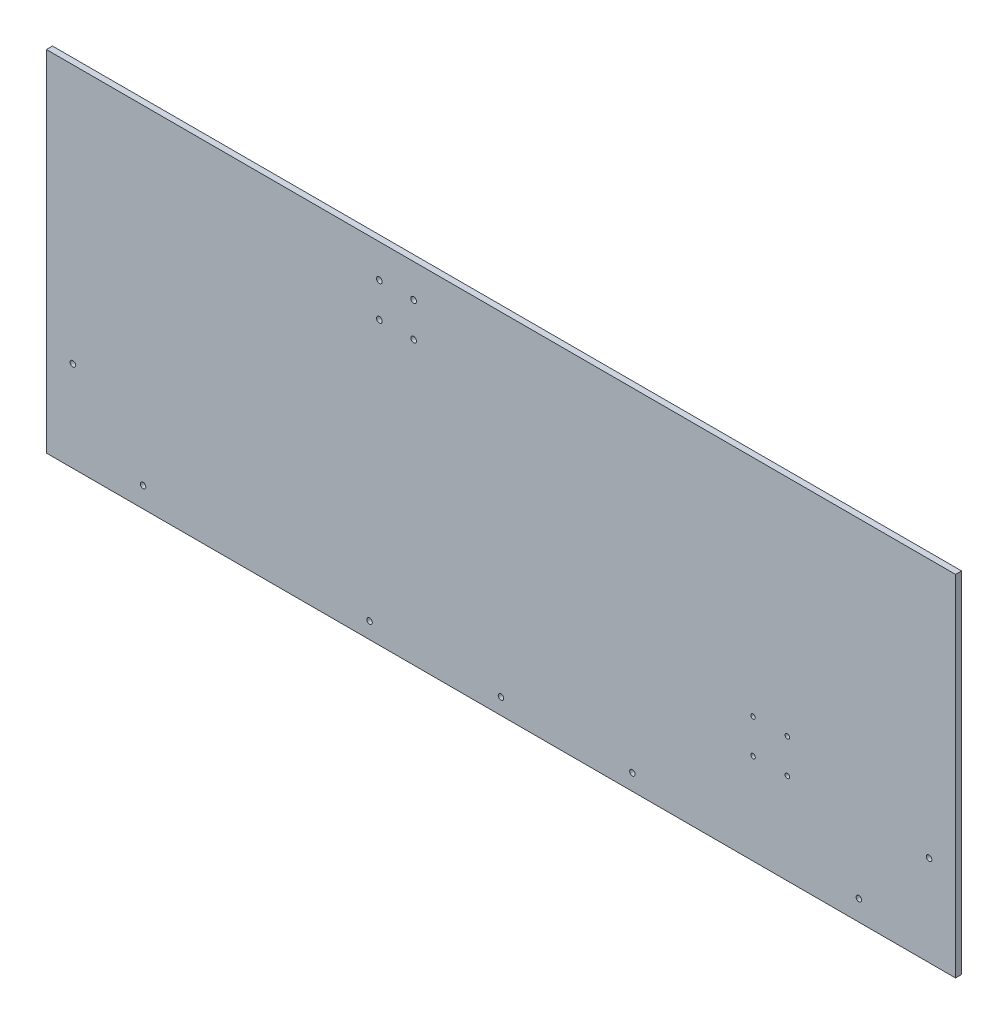
SolidWorks part; units mm, degrees
ref_plane "Front Plane" through (0, 0, 0) normal (0, 0, 1) x (1, 0, 0)
ref_plane "Top Plane" through (0, 0, 0) normal (0, 1, 0) x (1, 0, 0)
ref_plane "Right Plane" through (0, 0, 0) normal (1, 0, 0) x (0, 0, -1)
sketch "Sketch1" plane through (0, 0, 0) normal (0, 0, 1) x (1, 0, 0)
  line L1 (-357.1875, -137.3187) -> (357.1875, -137.3187)
  line L2 (-357.1875, -137.3187) -> (-357.1875, 137.3188)
  line L3 (-357.1875, 137.3188) -> (357.1875, 137.3188)
  line L4 (357.1875, -137.3187) -> (357.1875, 137.3188)
  line L5 (-357.1875, -137.3187) -> (357.1875, 137.3188) construction
  line L6 (-357.1875, 137.3188) -> (357.1875, -137.3187) construction
  point P0 (0, 0)
  dimension "D1" = 714.375
  dimension "D2" = 274.6375
extrude "Boss-Extrude1" add sketch "Sketch1" along normal blind 4.7625
sketch "Sketch2" plane through (0, 0, 4.7625) normal (0, 0, 1) x (1, 0, 0)
  line L0 (-357.1875, -137.3187) -> (-357.1875, -73.8187) construction
  line L1 (-357.1875, 137.3188) -> (-357.1875, -137.3187) construction
  line L2 (-357.1875, -105.5687) -> (357.1875, -105.5687) construction
  line L3 (12.286, -89.5705) -> (10.3514, -91.5051)
  line L4 (0, -105.5687) -> (0, -137.3187) construction
  line L5 (-357.1875, -137.3187) -> (357.1875, -137.3187) construction
  line L6 (357.1875, -137.3187) -> (357.1875, 137.3188) construction
  line L7 (0, -105.5687) -> (14.1421, -91.4266) construction
  line L8 (14.1421, -91.4266) -> (12.286, -89.5705) construction
  line L9 (12.286, -89.5705) -> (15.9983, -93.2828) construction
  line L10 (15.9983, -93.2828) -> (14.0637, -95.2174)
  line L11 (15.9983, -117.8547) -> (14.0637, -115.9201)
  line L12 (12.286, -121.567) -> (10.3514, -119.6324)
  line L13 (0, -105.5687) -> (14.1421, -119.7109) construction
  line L14 (14.1421, -119.7109) -> (15.9983, -117.8547) construction
  line L15 (15.9983, -117.8547) -> (12.286, -121.567) construction
  line L16 (-12.286, -121.567) -> (-10.3514, -119.6324)
  line L17 (-15.9983, -117.8547) -> (-14.0637, -115.9201)
  line L18 (0, -105.5687) -> (-14.1421, -119.7109) construction
  line L19 (-14.1421, -119.7109) -> (-12.286, -121.567) construction
  line L20 (-12.286, -121.567) -> (-15.9983, -117.8547) construction
  line L21 (-15.9983, -93.2828) -> (-14.0637, -95.2174)
  line L22 (-12.286, -89.5705) -> (-10.3514, -91.5051)
  line L23 (0, -105.5687) -> (-14.1421, -91.4266) construction
  line L24 (-14.1421, -91.4266) -> (-15.9983, -93.2828) construction
  line L25 (-15.9983, -93.2828) -> (-12.286, -89.5705) construction
  line L26 (0, -105.5687) -> (-317.5, -105.5687) construction
  line L27 (0, -105.5687) -> (317.5, -105.5687) construction
  line L28 (-317.5, -105.5687) -> (0, -105.5687) construction
  line L29 (-158.75, -105.5687) -> (-158.75, 137.3188) construction
  line L30 (357.1875, 137.3188) -> (-357.1875, 137.3188) construction
  line L31 (317.5, -105.5687) -> (0, -105.5687) construction
  line L32 (158.75, -105.5687) -> (158.75, 137.3188) construction
  line L33 (-301.5017, -93.2828) -> (-305.214, -89.5705) construction
  line L34 (-303.3579, -91.4266) -> (-301.5017, -93.2828) construction
  line L35 (-317.5, -105.5687) -> (-303.3579, -91.4266) construction
  line L36 (-305.214, -121.567) -> (-301.5017, -117.8547) construction
  line L37 (-303.3579, -119.7109) -> (-305.214, -121.567) construction
  line L38 (-317.5, -105.5687) -> (-303.3579, -119.7109) construction
  line L39 (-333.4983, -117.8547) -> (-329.786, -121.567) construction
  line L40 (-331.6421, -119.7109) -> (-333.4983, -117.8547) construction
  line L41 (-317.5, -105.5687) -> (-331.6421, -119.7109) construction
  line L42 (-329.786, -89.5705) -> (-333.4983, -93.2828) construction
  line L43 (-331.6421, -91.4266) -> (-329.786, -89.5705) construction
  line L44 (-317.5, -105.5687) -> (-331.6421, -91.4266) construction
  line L45 (-317.5, -105.5687) -> (-317.5, -137.3187) construction
  line L46 (-305.214, -89.5705) -> (-307.1486, -91.5051)
  line L47 (-301.5017, -93.2828) -> (-303.4363, -95.2174)
  line L48 (-301.5017, -117.8547) -> (-303.4363, -115.9201)
  line L49 (-305.214, -121.567) -> (-307.1486, -119.6324)
  line L50 (-329.786, -121.567) -> (-327.8514, -119.6324)
  line L51 (-333.4983, -117.8547) -> (-331.5637, -115.9201)
  line L52 (-333.4983, -93.2828) -> (-331.5637, -95.2174)
  line L53 (-329.786, -89.5705) -> (-327.8514, -91.5051)
  line L54 (333.4983, -93.2828) -> (329.786, -89.5705) construction
  line L55 (331.6421, -91.4266) -> (333.4983, -93.2828) construction
  line L56 (317.5, -105.5687) -> (331.6421, -91.4266) construction
  line L57 (329.786, -121.567) -> (333.4983, -117.8547) construction
  line L58 (331.6421, -119.7109) -> (329.786, -121.567) construction
  line L59 (317.5, -105.5687) -> (331.6421, -119.7109) construction
  line L60 (301.5017, -117.8547) -> (305.214, -121.567) construction
  line L61 (303.3579, -119.7109) -> (301.5017, -117.8547) construction
  line L62 (317.5, -105.5687) -> (303.3579, -119.7109) construction
  line L63 (305.214, -89.5705) -> (301.5017, -93.2828) construction
  line L64 (303.3579, -91.4266) -> (305.214, -89.5705) construction
  line L65 (317.5, -105.5687) -> (303.3579, -91.4266) construction
  line L66 (317.5, -105.5687) -> (317.5, -137.3187) construction
  line L67 (329.786, -89.5705) -> (327.8514, -91.5051)
  line L68 (333.4983, -93.2828) -> (331.5637, -95.2174)
  line L69 (333.4983, -117.8547) -> (331.5637, -115.9201)
  line L70 (329.786, -121.567) -> (327.8514, -119.6324)
  line L71 (305.214, -121.567) -> (307.1486, -119.6324)
  line L72 (301.5017, -117.8547) -> (303.4363, -115.9201)
  line L73 (301.5017, -93.2828) -> (303.4363, -95.2174)
  line L74 (305.214, -89.5705) -> (307.1486, -91.5051)
  arc A0 (-14.0637, -95.2174) -> (-14.0637, -115.9201) centre (0, -105.5687) ccw
  arc A1 (15.9983, -93.2828) -> (12.286, -89.5705) centre (14.1421, -91.4266) ccw
  arc A2 (12.286, -121.567) -> (15.9983, -117.8547) centre (14.1421, -119.7109) ccw
  arc A3 (-15.9983, -117.8547) -> (-12.286, -121.567) centre (-14.1421, -119.7109) ccw
  arc A4 (-12.286, -89.5705) -> (-15.9983, -93.2828) centre (-14.1421, -91.4266) ccw
  arc A5 (10.3514, -91.5051) -> (-10.3514, -91.5051) centre (0, -105.5687) ccw
  arc A6 (14.0637, -115.9201) -> (14.0637, -95.2174) centre (0, -105.5687) ccw
  arc A7 (-10.3514, -119.6324) -> (10.3514, -119.6324) centre (0, -105.5687) ccw
  arc A8 (-307.1486, -119.6324) -> (-327.8514, -119.6324) centre (-317.5, -105.5687) cw
  arc A9 (-331.5637, -115.9201) -> (-331.5637, -95.2174) centre (-317.5, -105.5687) cw
  arc A10 (-327.8514, -91.5051) -> (-307.1486, -91.5051) centre (-317.5, -105.5687) cw
  arc A11 (-305.214, -89.5705) -> (-301.5017, -93.2828) centre (-303.3579, -91.4266) cw
  arc A12 (-301.5017, -117.8547) -> (-305.214, -121.567) centre (-303.3579, -119.7109) cw
  arc A13 (-329.786, -121.567) -> (-333.4983, -117.8547) centre (-331.6421, -119.7109) cw
  arc A14 (-333.4983, -93.2828) -> (-329.786, -89.5705) centre (-331.6421, -91.4266) cw
  arc A15 (-303.4363, -95.2174) -> (-303.4363, -115.9201) centre (-317.5, -105.5687) cw
  arc A16 (327.8514, -119.6324) -> (307.1486, -119.6324) centre (317.5, -105.5687) cw
  arc A17 (303.4363, -115.9201) -> (303.4363, -95.2174) centre (317.5, -105.5687) cw
  arc A18 (307.1486, -91.5051) -> (327.8514, -91.5051) centre (317.5, -105.5687) cw
  arc A19 (329.786, -89.5705) -> (333.4983, -93.2828) centre (331.6421, -91.4266) cw
  arc A20 (333.4983, -117.8547) -> (329.786, -121.567) centre (331.6421, -119.7109) cw
  arc A21 (305.214, -121.567) -> (301.5017, -117.8547) centre (303.3579, -119.7109) cw
  arc A22 (301.5017, -93.2828) -> (305.214, -89.5705) centre (303.3579, -91.4266) cw
  arc A23 (331.5637, -95.2174) -> (331.5637, -115.9201) centre (317.5, -105.5687) cw
  point P37 (0, -105.5688)
  dimension "D2" = 34.925
  dimension "D3" = 5.25
  dimension "D1" = 63.5
  dimension "D4" = 20
  dimension "D5" = 45
  dimension "D7" = 317.5
  dimension "D8" = 317.5
  dimension "D6" = 4
extrude "Cut-Extrude1" cut sketch "Sketch2" against normal through all
sketch "Sketch4" plane through (0, 0, 4.7625) normal (0, 0, 1) x (1, 0, 0)
  line L0 (0, 0) -> (0, 137.3188) construction
  line L1 (357.1875, 137.3188) -> (-357.1875, 137.3188) construction
  line L2 (-357.1875, 130.9688) -> (357.1875, 130.9688) construction
  line L3 (-357.1875, 137.3188) -> (-357.1875, -137.3187) construction
  line L4 (357.1875, -137.3187) -> (357.1875, 137.3188) construction
  line L5 (-357.1875, 130.9688) -> (0, 130.9688) construction
  line L6 (0, 130.9688) -> (357.1875, 130.9688) construction
  line L7 (-357.1875, 130.9688) -> (0, 130.9688) construction
  line L8 (0, 130.9688) -> (357.1875, 130.9688) construction
  line L9 (-279.4, 88.4238) -> (-279.4, 97.3138) construction
  line L10 (0, 67.4688) -> (357.1875, 67.4688) construction
  line L11 (357.1875, 67.4688) -> (-357.1875, 67.4687) construction
  line L12 (279.4, 86.8616) -> (279.4, 98.8759) construction
  line L13 (279.4, 88.4238) -> (279.4, 97.3138) construction
  line L14 (277.1521, 88.4238) -> (277.1521, 97.3138)
  line L15 (281.6479, 88.4238) -> (281.6479, 97.3138)
  line L16 (-277.1521, 88.4238) -> (-277.1521, 97.3138)
  line L17 (-281.6479, 88.4238) -> (-281.6479, 97.3138)
  line L18 (-279.4, 92.8688) -> (-279.4, 67.4688) construction
  line L19 (279.4, 92.8688) -> (279.4, 67.4688) construction
  line L20 (-279.4, 86.8616) -> (-279.4, 98.8759) construction
  arc A0 (277.1521, 88.4238) -> (281.6479, 88.4238) centre (279.4, 88.4238) ccw
  arc A1 (281.6479, 97.3138) -> (277.1521, 97.3138) centre (279.4, 97.3138) ccw
  arc A2 (-277.1521, 88.4238) -> (-281.6479, 88.4238) centre (-279.4, 88.4238) cw
  arc A3 (-281.6479, 97.3138) -> (-277.1521, 97.3138) centre (-279.4, 97.3138) cw
  point P21 (279.4, 92.8688)
  point P26 (-279.4, 92.8688)
  dimension "D1" = 6.35
  dimension "D2" = 63.5
  dimension "D3" = 8.89
  dimension "D4" = 4.4958
  dimension "D6" = 279.4
  dimension "D7" = 25.4
extrude "Cut-Extrude3" cut sketch "Sketch4" against normal through all
sketch "Sketch5" plane through (0, 0, 4.7625) normal (0, 0, 1) x (1, 0, 0)
  line L0 (0, 137.3188) -> (0, -137.3187) construction
  line L1 (357.1875, 137.3188) -> (-357.1875, 137.3188) construction
  line L2 (-357.1875, -137.3187) -> (357.1875, -137.3187) construction
  line L3 (-357.1875, -73.8187) -> (357.1875, -73.8187) construction
  line L4 (-357.1875, 137.3188) -> (-357.1875, -137.3187) construction
  line L5 (357.1875, -137.3187) -> (357.1875, 137.3188) construction
  line L6 (-357.1875, -73.8187) -> (-357.1875, -137.3187) construction
  line L7 (-357.1875, -105.5687) -> (357.1875, -105.5687) construction
  line L8 (0, -137.3187) -> (0, -105.5687) construction
  circle A0 centre (-127, -105.5687) radius 2.1527
  circle A1 centre (-215.9, -105.5687) radius 2.1527
  circle A2 centre (215.9, -105.5687) radius 2.1527
  circle A3 centre (127, -105.5687) radius 2.1527
  dimension "D2" = 4.3053
  dimension "D1" = 63.5
  dimension "D3" = 127
  dimension "D4" = 215.9
extrude "Cut-Extrude4" cut sketch "Sketch5" against normal up to next
sketch "Sketch7" plane through (357.1875, 0, 0) normal (1, 0, 0) x (0, 0, -1)
  line L1 (-4.7625, 137.3188) -> (0, 137.3188)
  line L2 (-4.7625, 137.3188) -> (-4.7625, -137.3187)
  line L3 (-4.7625, -137.3187) -> (0, -137.3187)
  line L4 (0, 137.3188) -> (0, -137.3187)
extrude "Boss-Extrude2" add sketch "Sketch7" against normal up to next
hole_wizard "#8 Clearance Hole1" positions "Sketch9" profile "Sketch8" hole size "#8" standard "ANSI Inch"
sketch "Sketch9" plane through (0, 0, 4.7625) normal (0, 0, 1) x (1, 0, 0)
  line L0 (-357.1875, 137.3188) -> (-357.1875, -137.3187) construction
  line L1 (-357.1875, -137.3187) -> (357.1875, -137.3187) construction
  line L2 (357.1875, -137.3187) -> (357.1875, 137.3188) construction
  point P0 (-336.4154, -66.1327)
  point P2 (-281.239, -121.3091)
  point P4 (281.239, -121.3091)
  point P6 (336.4154, -66.1327)
  dimension "D1" = 20.7721
  dimension "D2" = 75.9485
  dimension "D3" = 71.186
  dimension "D4" = 16.0096
  dimension "D5" = 20.7721
  dimension "D6" = 75.9485
sketch "Sketch8" plane through (-336.4154, -66.1327, 4.7625) normal (1, 0, 0) x (0, -1, 0)
  line L0 (0, 0) -> (0, 75.7154)
  line L1 (0, 75.7154) -> (2.1526, 74.422)
  line L2 (2.1526, 74.422) -> (2.1526, 0)
  line L5 (2.1526, 0) -> (0, 0)
  line L10 (0, 75.7154) -> (-2.1527, 74.422) construction
  line L11 (0, -6.35) -> (0, 107.95) construction
  dimension "Hole Dia." = 4.3053
  dimension "Hole Depth" = 74.422
  dimension "Drill Angle" = 118
hole_wizard "#8 Clearance Hole2" positions "Sketch12" profile "Sketch11" hole size "#8" standard "ANSI Inch"
sketch "Sketch12" plane through (0, 0, 4.7625) normal (0, 0, 1) x (1, 0, 0)
  line L0 (-357.1875, -137.3187) -> (357.1875, -137.3187) construction
  point P0 (-103.251, -124.6187)
  point P2 (0, -124.6187)
  point P4 (103.251, -124.6187)
  dimension "D1" = 12.7
  dimension "D2" = 103.251
  dimension "D3" = 103.251
sketch "Sketch11" plane through (-103.251, -124.6187, 4.7625) normal (1, 0, 0) x (0, -1, 0)
  line L0 (0, 0) -> (0, 75.7154)
  line L1 (0, 75.7154) -> (2.1526, 74.422)
  line L2 (2.1526, 74.422) -> (2.1526, 0)
  line L5 (2.1526, 0) -> (0, 0)
  line L10 (0, 75.7154) -> (-2.1527, 74.422) construction
  line L11 (0, -6.35) -> (0, 107.95) construction
  dimension "Hole Dia." = 4.3053
  dimension "Hole Depth" = 74.422
  dimension "Drill Angle" = 118
hole_wizard "#8 Clearance Hole3" positions "Sketch15" profile "Sketch14" hole size "#8" standard "ANSI Inch"
sketch "Sketch15" plane through (0, 0, 4.7625) normal (0, 0, 1) x (1, 0, 0)
  line L0 (357.1875, 137.3188) -> (-357.1875, 137.3188) construction
  line L1 (-357.1875, 137.3188) -> (-357.1875, -137.3187) construction
  point P0 (-95.5675, 111.1568)
  point P2 (-68.6435, 111.1568)
  point P4 (-95.5675, 84.2328)
  point P6 (-68.6435, 84.2328)
  dimension "D1" = 26.162
  dimension "D2" = 26.924
  dimension "D3" = 26.924
  dimension "D4" = 261.62
sketch "Sketch14" plane through (-95.5675, 111.1568, 4.7625) normal (1, 0, 0) x (0, -1, 0)
  line L0 (0, 0) -> (0, 75.7727)
  line L1 (0, 75.7727) -> (2.2479, 74.422)
  line L2 (2.2479, 74.422) -> (2.2479, 0)
  line L5 (2.2479, 0) -> (0, 0)
  line L10 (0, 75.7727) -> (-2.2479, 74.422) construction
  line L11 (0, -6.35) -> (0, 107.95) construction
  dimension "Hole Dia." = 4.4958
  dimension "Hole Depth" = 74.422
  dimension "Drill Angle" = 118
sketch "Sketch16" plane through (0, 0, 4.7625) normal (0, 0, 1) x (1, 0, 0)
  circle A0 centre (198.0481, -38.9489) radius 1.778
  circle A1 centre (224.9889, -38.9489) radius 1.778
  circle A2 centre (224.9889, -65.8896) radius 1.778
  circle A3 centre (198.0481, -65.8896) radius 1.778
extrude "Cut-Extrude5" cut sketch "Sketch16" against normal blind 4.7625
